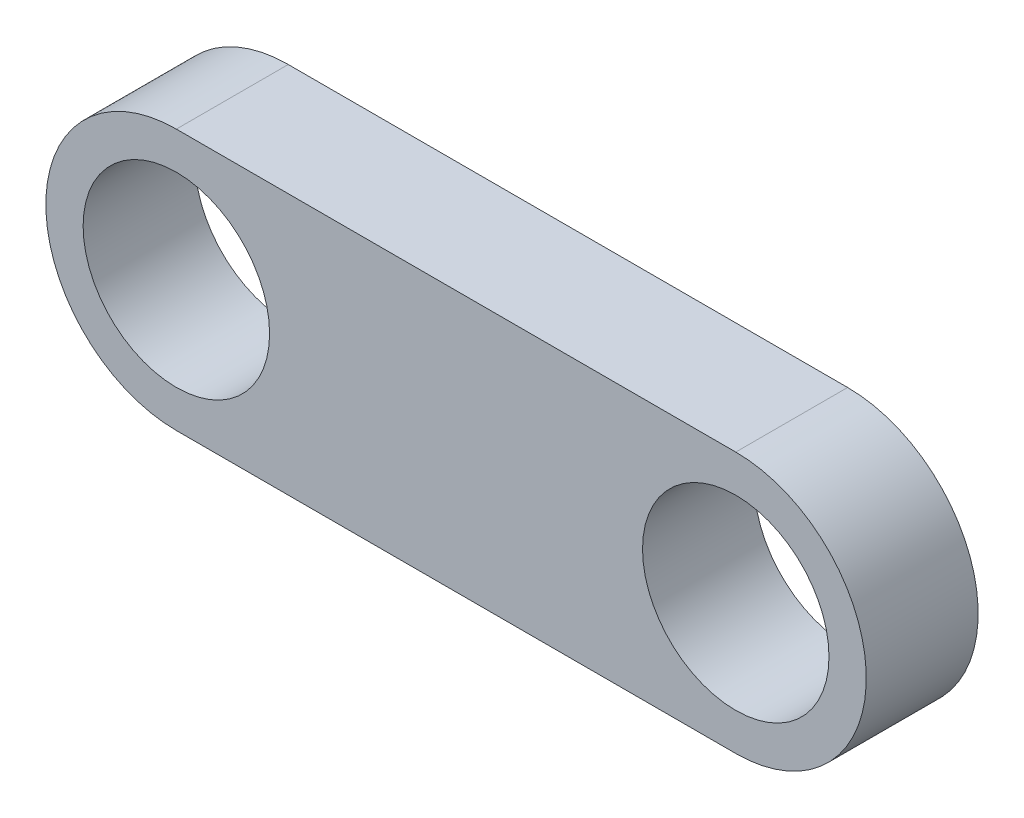
SolidWorks part; units mm, degrees
ref_plane "Front Plane" through (0, 0, 0) normal (0, 0, 1) x (1, 0, 0)
ref_plane "Top Plane" through (0, 0, 0) normal (0, 1, 0) x (1, 0, 0)
ref_plane "Right Plane" through (0, 0, 0) normal (1, 0, 0) x (0, 0, -1)
sketch "Sketch1" plane through (0, 0, 0) normal (0, 0, 1) x (1, 0, 0)
  line L0 (-13.8462, 0) -> (16.1538, 0) construction
  line L1 (-13.8462, 7) -> (16.1538, 7)
  line L2 (-13.8462, -7) -> (16.1538, -7)
  arc A0 (-13.8462, 7) -> (-13.8462, -7) centre (-13.8462, 0) ccw
  arc A1 (16.1538, -7) -> (16.1538, 7) centre (16.1538, 0) ccw
  point P3 (1.1538, 0)
  dimension "D2" = 7
  dimension "D1" = 30
extrude "Boss-Extrude1" add sketch "Sketch1" along normal blind 6
sketch "Sketch2" plane through (0, 0, 6) normal (0, 0, 1) x (1, 0, 0)
  line L0 (-1020.8462, 0) -> (48979.1538, 0) construction
  line L1 (-13.8462, -993) -> (-13.8462, 49007) construction
  line L3 (0, -1000) -> (0, 49000) construction
  line L4 (16.1538, -993) -> (16.1538, 49007) construction
  arc A0 (-13.8462, 7) -> (-13.8462, -7) centre (-13.8462, 0) ccw construction
  circle A1 centre (-13.8462, 0) radius 5
  circle A2 centre (16.1538, 0) radius 5
  point P6 (-20.8462, 0)
  dimension "D1" = 10
  dimension "D2" = 10
extrude "Cut-Extrude1" cut sketch "Sketch2" against normal blind 6
scale "Scale1" scale about centroid uniform scaling yes scale factor 0.3
